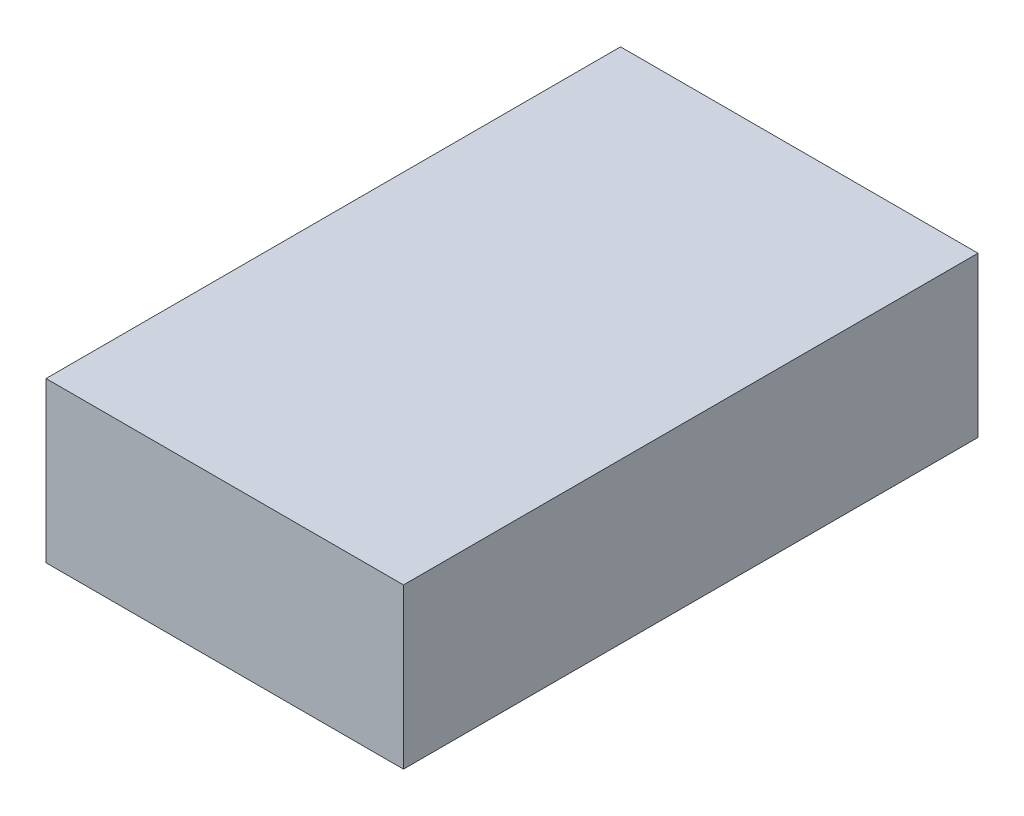
SolidWorks part; units mm, degrees
ref_plane "Front Plane" through (0, 0, 0) normal (0, 0, 1) x (1, 0, 0)
ref_plane "Top Plane" through (0, 0, 0) normal (0, 1, 0) x (1, 0, 0)
ref_plane "Right Plane" through (0, 0, 0) normal (1, 0, 0) x (0, 0, -1)
sketch "Sketch1" plane through (0, 0, 0) normal (0, 0, 1) x (1, 0, 0)
  line L1 (0, 0) -> (71.12, 0)
  line L2 (0, 0) -> (0, 31.75)
  line L3 (0, 31.75) -> (71.12, 31.75)
  line L4 (71.12, 0) -> (71.12, 31.75)
  dimension "D1" = 71.12
  dimension "D2" = 31.75
extrude "Boss-Extrude1" add sketch "Sketch1" along normal blind 114.3
